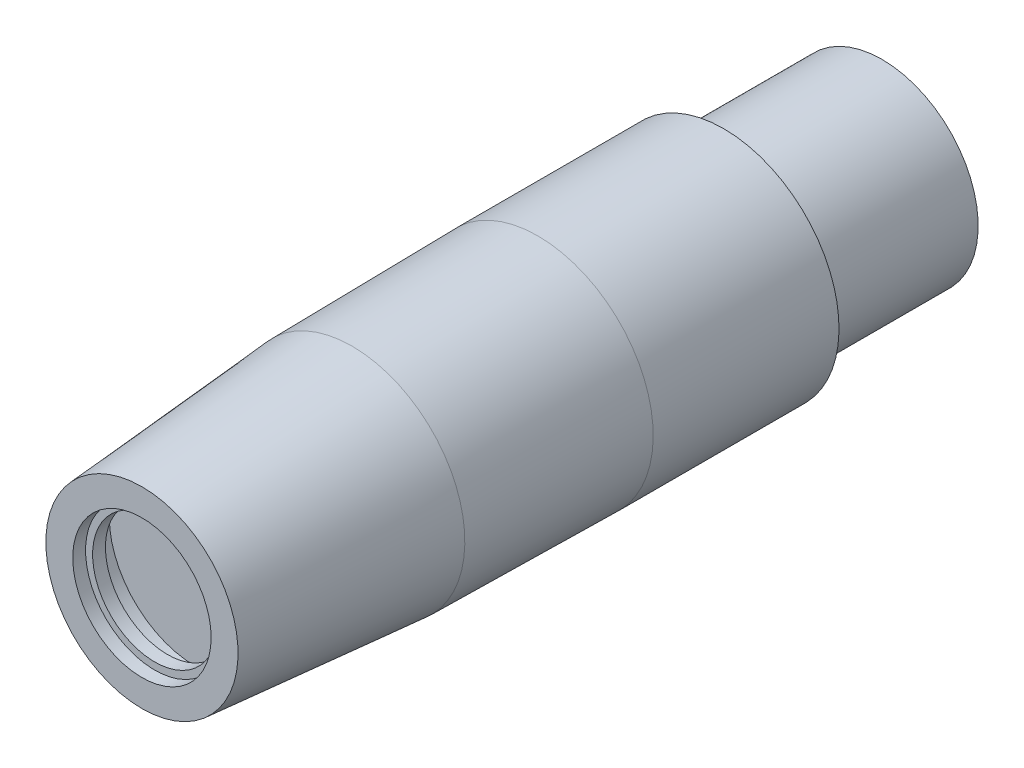
SolidWorks part; units mm, degrees
ref_plane "Front Plane" through (0, 0, 0) normal (0, 0, 1) x (1, 0, 0)
ref_plane "Top Plane" through (0, 0, 0) normal (0, 1, 0) x (1, 0, 0)
ref_plane "Right Plane" through (0, 0, 0) normal (1, 0, 0) x (0, 0, -1)
sketch "Sketch1" plane through (0, 0, 0) normal (1, 0, 0) x (0, 0, -1)
  line L0 (0, 0) -> (0, 7.5)
  line L1 (0, 7.5) -> (16.4, 8.8)
  line L2 (16.4, 8.8) -> (30.9, 9)
  line L3 (30.9, 9) -> (45.4, 9)
  line L4 (45.4, 9) -> (45.4, 7.5)
  line L5 (45.4, 7.5) -> (57.76, 7.5)
  line L6 (57.76, 7.5) -> (57.76, 6.125)
  line L7 (57.76, 6.125) -> (58.51, 6.125)
  line L8 (58.51, 6.125) -> (58.51, 0)
  line L9 (58.51, 0) -> (0, 0)
  dimension "D1" = 16.4
  dimension "D2" = 14.5
  dimension "D3" = 14.5
  dimension "D4" = 12.36
  dimension "D5" = 0.75
  dimension "D6" = 7.5
  dimension "D7" = 8.8
  dimension "D8" = 9
  dimension "D9" = 7.5
  dimension "D10" = 6.125
revolve "Revolve1" add sketch "Sketch1" angle 360 about L9
sketch "Sketch2" plane through (0, 0, -58.51) normal (0, 0, -1) x (-1, 0, 0)
  line L0 (-3.836, 4.775) -> (3.836, 4.775)
  line L1 (0, 6.125) -> (0, -6.125) construction
  circle A0 centre (0, 0) radius 6.125 construction
  circle A1 centre (0, 0) radius 6.125 construction
  arc A2 (-3.836, 4.775) -> (3.836, 4.775) centre (0, 0) cw
  point P10 (0, 4.775)
  dimension "D1" = 1.35
extrude "Cut-Extrude1" cut sketch "Sketch2" against normal up to surface (0.75 mm away) up to face at (0, 7.5, -57.76)
sketch "Sketch3" plane through (0, 0, 0) normal (0, 0, 1) x (1, 0, 0)
  circle A0 centre (0, 0) radius 5.4
  dimension "D1" = 10.8
extrude "Cut-Extrude2" cut sketch "Sketch3" against normal blind 1
sketch "Sketch4" plane through (0, 0, -1) normal (0, 0, 1) x (1, 0, 0)
  circle A0 centre (0, 0) radius 4.85
  dimension "D1" = 9.7
extrude "Cut-Extrude3" cut sketch "Sketch4" against normal blind 1
sketch "Sketch5" plane through (0, 0, -2) normal (0, 0, 1) x (1, 0, 0)
  circle A0 centre (0, 0) radius 6.75
  dimension "D1" = 13.5
extrude "Cut-Extrude4" cut sketch "Sketch5" against normal blind 2.2
